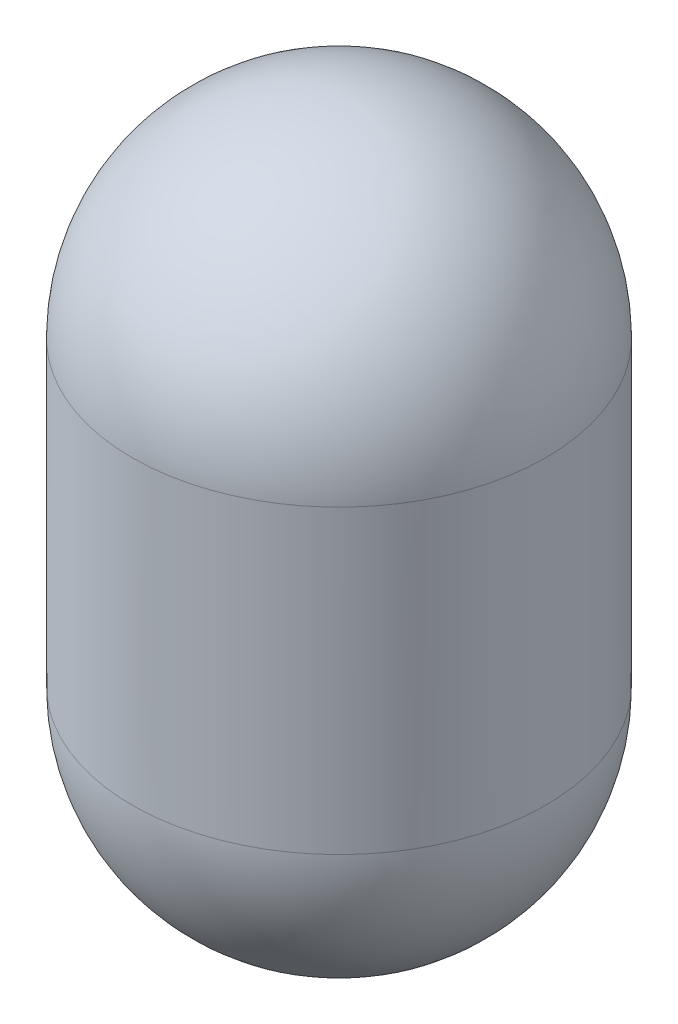
SolidWorks part; units mm, degrees
ref_plane "Front" through (0, 0, 0) normal (0, 0, 1) x (1, 0, 0)
ref_plane "Top" through (0, 0, 0) normal (0, 1, 0) x (1, 0, 0)
ref_plane "Right" through (0, 0, 0) normal (1, 0, 0) x (0, 0, -1)
sketch "Sketch2" plane through (0, 0, 0) normal (0, 1, 0) x (1, 0, 0)
  circle A0 centre (0, 0) radius 69.85
  dimension "D1" = 139.7
extrude "Extrude1" add sketch "Sketch2" along normal blind 101.6
sketch "Sketch3" plane through (0, 101.6, 0) normal (0, 1, 0) x (-1, 0, 0)
  point P0 (0, 0)
sketch "Sketch4" plane through (0, 0, 0) normal (0, -1, 0) x (1, 0, 0)
  line L0 (0, -53.34) -> (0, 53.34) construction
  point P0 (0, 0)
sketch "Sketch5" plane through (0, 0, 0) normal (0, 0, 1) x (1, 0, 0)
  line L0 (69.85, 101.6) -> (-69.85, 101.6) construction
  line L1 (0, 171.45) -> (0, 101.6)
  line L2 (0, 101.6) -> (-69.85, 101.6)
  line L6 (0, 101.6) -> (0, 0) construction
  arc A0 (-69.85, 101.6) -> (0, 171.45) centre (0, 101.6) cw
revolve "Revolve1" add sketch "Sketch5" angle 360 about L6
sketch "Sketch6" plane through (0, 0, 0) normal (0, 0, 1) x (1, 0, 0)
  line L0 (0, -69.85) -> (0, 0)
  line L1 (0, 0) -> (-69.85, 0)
  line L2 (0, 0) -> (0, 101.6) construction
  arc A0 (-69.85, 0) -> (0, -69.85) centre (0, 0) ccw
revolve "Revolve2" add sketch "Sketch6" angle 360 about L2
